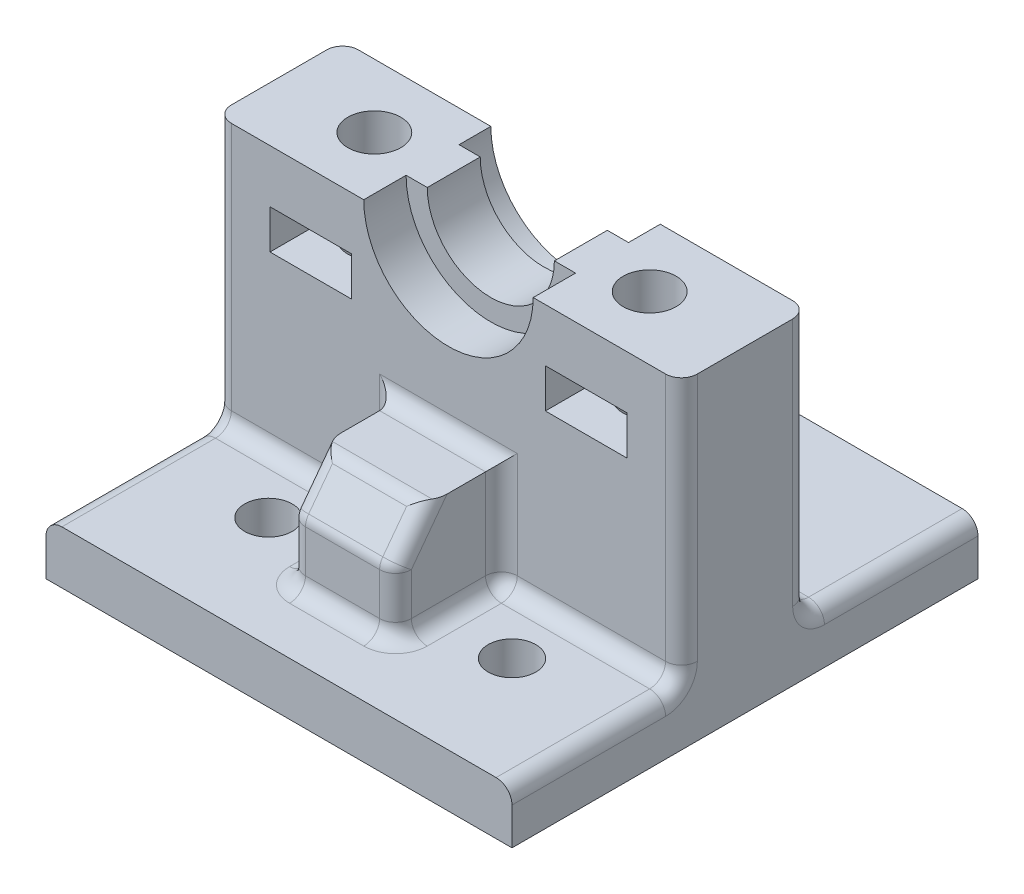
SolidWorks part; units mm, degrees
ref_plane "Front Plane" through (0, 0, 0) normal (0, 0, 1) x (1, 0, 0)
ref_plane "Top Plane" through (0, 0, 0) normal (0, 1, 0) x (1, 0, 0)
ref_plane "Right Plane" through (0, 0, 0) normal (1, 0, 0) x (0, 0, -1)
sketch "Sketch1" plane through (0, 0, 0) normal (0, 1, 0) x (1, 0, 0)
  line L1 (0, 0) -> (44, 0)
  line L2 (0, 0) -> (0, 44)
  line L3 (0, 44) -> (44, 44)
  line L4 (44, 0) -> (44, 44)
  dimension "D1" = 44
  dimension "D2" = 44
extrude "Boss-Extrude1" add sketch "Sketch1" along normal blind 5
sketch "Sketch2" plane through (0, 5, 0) normal (0, 1, 0) x (1, 0, 0)
  line L0 (0, 44) -> (0, 0) construction
  line L1 (0, 28) -> (44, 28)
  line L2 (0, 28) -> (0, 16)
  line L3 (0, 16) -> (44, 16)
  line L4 (44, 28) -> (44, 16)
  line L5 (44, 0) -> (44, 44) construction
  line L6 (0, 0) -> (44, 0) construction
  point P10 (44, 22)
  dimension "D1" = 22
  dimension "D2" = 12
extrude "Boss-Extrude2" add sketch "Sketch2" along normal blind 25
sketch "Sketch3" plane through (0, 30, 0) normal (0, 1, 0) x (1, 0, 0)
  line L0 (44, 22) -> (0, 22) construction
  line L1 (44, 16) -> (44, 28) construction
  line L2 (0, 28) -> (0, 16) construction
  circle A0 centre (35, 22) radius 2.5
  circle A1 centre (9, 22) radius 2.5
  point P10 (22, 22)
  dimension "D1" = 5
  dimension "D2" = 5
  dimension "D3" = 13
  dimension "D4" = 26
extrude "Cut-Extrude1" cut sketch "Sketch3" against normal blind 15
sketch "Sketch4" plane through (0, 0, -16) normal (0, 0, 1) x (1, 0, 0)
  line L0 (0, 30) -> (44, 30) construction
  line L1 (38.85, 21.3) -> (31.15, 21.3)
  line L2 (38.85, 21.3) -> (38.85, 25)
  line L3 (38.85, 25) -> (31.15, 25)
  line L4 (31.15, 21.3) -> (31.15, 25)
  line L5 (12.85, 21.3) -> (5.15, 21.3)
  line L6 (12.85, 21.3) -> (12.85, 25)
  line L7 (12.85, 25) -> (5.15, 25)
  line L8 (5.15, 21.3) -> (5.15, 25)
  circle A0 centre (22, 30) radius 6
  point P8 (35, 21.3)
  point P11 (22, 30)
  point P12 (9, 21.3)
  line M8 (44, 30) -> (0, 30)
  dimension "D6" = 12
  dimension "D1" = 7.7
  dimension "D2" = 3.7
  dimension "D3" = 13
  dimension "D4" = 26
  dimension "D5" = 5
extrude "Cut-Extrude2" cut sketch "Sketch4" against normal through all contours L8 L5 L6 L7 | A0 M8 | A0 M8 | L1 L4 L3 L2
sketch "Sketch6" plane through (0, 0, -16) normal (0, 0, 1) x (1, 0, 0)
  circle A0 centre (22, 30) radius 8
  dimension "D1" = 16
extrude "Cut-Extrude3" cut sketch "Sketch6" against normal blind 4
sketch "Sketch7" plane through (0, 0, -28) normal (0, 0, -1) x (-1, 0, 0)
  line L0 (-30, 30) -> (-14, 30)
  arc A0 (-30, 30) -> (-14, 30) centre (-22, 30) ccw construction
  arc A1 (-30, 30) -> (-14, 30) centre (-22, 30) ccw
extrude "Cut-Extrude4" cut sketch "Sketch7" against normal blind 3
ref_plane "Plane1" through (22, 0, 0) normal (1, 0, 0) x (0, 0, -1)
sketch "Sketch8" plane through (22, 0, 0) normal (1, 0, 0) x (0, 0, -1)
  line L0 (16, 5) -> (0, 5) construction
  line L1 (16, 5) -> (6, 5)
  line L2 (6, 5) -> (6, 11)
  line L3 (6, 11) -> (9, 15)
  line L4 (16, 5) -> (16, 15)
  line L5 (16, 15) -> (9, 15)
  dimension "D1" = 10
  dimension "D2" = 10
  dimension "D3" = 6
  dimension "D4" = 7
extrude "Boss-Extrude3" add sketch "Sketch8" along normal mid plane 10
sketch "Sketch10" plane through (0, 5, 0) normal (0, 1, 0) x (1, 0, 0)
  line L0 (35.6141, 10.5) -> (6.4809, 10.5) construction
  line L3 (45.867, 33.5) -> (-16.9652, 33.5) construction
  line L6 (22, 0) -> (22, 44) construction
  line L7 (0, 0) -> (44, 0) construction
  line L8 (44, 44) -> (0, 44) construction
  line L9 (44, 22) -> (0, 22) construction
  line L10 (44, 16) -> (44, 28) construction
  line L11 (0, 28) -> (0, 16) construction
  circle A0 centre (33.5, 10.5) radius 2.25
  circle A1 centre (10.5, 10.5) radius 2.25
  circle A2 centre (33.5, 33.5) radius 2.25
  circle A3 centre (10.5, 33.5) radius 2.25
  dimension "D1" = 4.5
  dimension "D4" = 23
  dimension "D5" = 11.5
  dimension "D6" = 23
  dimension "D7" = 11.5
  dimension "D2" = 11.5
  dimension "D3" = 23
extrude "Cut-Extrude5" cut sketch "Sketch10" against normal blind 10
fillet "Fillet2" radius 1.5 23 edges at (27, 5, -11) (17, 5, -11) (44, 5, -36) (0, 5, -36) (22, 11, -6) (27, 8, -6) (22, 5, -6) (17, 8, -6) (17, 10, -16) (27, 10, -16) (17, 13, -7.5) (27, 13, -7.5) (22, 15, -9) (22, 15, -16) (8.5, 5, -16) (35.5, 5, -16) (44, 17.5, -16) (44, 5, -8) (44, 17.5, -28) (0, 17.5, -16) (0, 5, -8) (22, 5, -28) (0, 17.5, -28)
